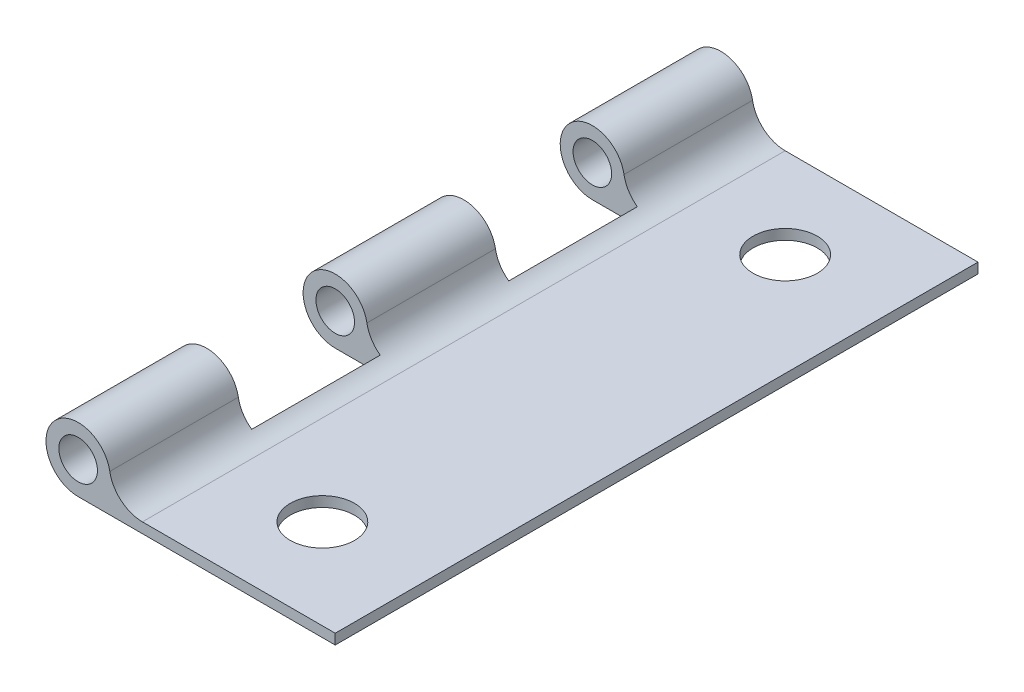
SolidWorks part; units mm, degrees
material "Aço cromo inoxidável"
ref_plane "Plano frontal" through (0, 0, 0) normal (0, 0, 1) x (1, 0, 0)
ref_plane "Plano superior" through (0, 0, 0) normal (0, 1, 0) x (1, 0, 0)
ref_plane "Plano direito" through (0, 0, 0) normal (1, 0, 0) x (0, 0, -1)
sketch "Esboço1" plane through (0, 0, 0) normal (0, 0, 1) x (1, 0, 0)
  line L0 (0, 0) -> (-20, 0)
  line L2 (-15, 0.8) -> (0, 0.8)
  line L3 (0, 0.8) -> (0, 0)
  arc A0 (-20, 0) -> (-19.9579, 4.9996) centre (-20, 2.5) cw
  arc A1 (-19.9579, 4.9996) -> (-17.5375, 2.9315) centre (-20, 2.5) cw
  arc A2 (-17.5375, 2.9315) -> (-15, 0.8) centre (-15, 3.3762) ccw
  circle A3 centre (-20, 2.5) radius 1.5
  circle A4 centre (-20, 2.5) radius 1.5 construction
  dimension "D4" = 20
  dimension "D5" = 1
  dimension "D1" = 0.8
  dimension "D3" = 5
extrude "Ressalto-extrusão1" add sketch "Esboço1" along normal blind 50
sketch "Esboço2" plane through (0, 0, 0) normal (0, -1, 0) x (1, 0, 0)
  line L0 (-22.5, 50) -> (-22.5, 0) construction
  line L1 (-22.5, 10) -> (-16.5, 10)
  line L2 (-22.5, 10) -> (-22.5, 20)
  line L3 (-22.5, 20) -> (-16.5, 20)
  line L4 (-16.5, 10) -> (-16.5, 20)
  line L5 (0, 50) -> (0, 0) construction
  line L6 (0, 50) -> (-15, 50) construction
  line L11 (-22.5, 30) -> (-22.5, 40)
  line L12 (-22.5, 30) -> (-16.5, 30)
  line L13 (-16.5, 30) -> (-16.5, 40)
  line L14 (-22.5, 40) -> (-16.5, 40)
  line L15 (-22.5, 0) -> (-17.5375, 0) construction
  line L16 (0, 25) -> (-6.2647, 25) construction
  line L17 (0, 50) -> (0, 0) construction
  line L18 (-22.5, 20) -> (-22.5, 30) [skipped]
  line L19 (-16.5, 20) -> (-16.5, 30) [skipped]
  line L20 (-22.5, 30) -> (-16.5, 30) [skipped]
  line L21 (-22.5, 20) -> (-16.5, 20) [skipped]
  circle A0 centre (-8, 43) radius 2.5
  circle A1 centre (-8, 7) radius 2.5
  dimension "D8" = 5
  dimension "D1" = 10
  dimension "D2" = 3
  dimension "D3" = 10
  dimension "D4" = 10
  dimension "D5" = 6
  dimension "D6" = 8
  dimension "D7" = 7
extrude "Corte-extrusão1" cut sketch "Esboço2" against normal through all
